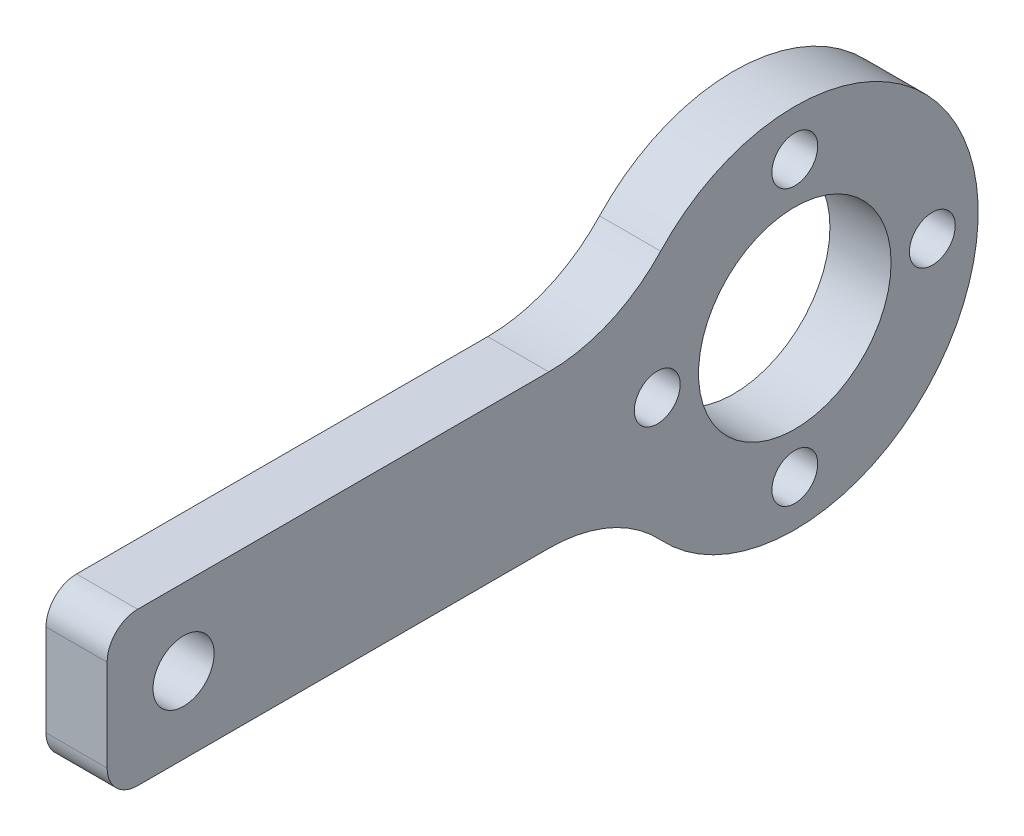
SolidWorks part; units mm, degrees
material "Thornel Mat VMA"
ref_plane "前视基准面" through (0, 0, 0) normal (0, 0, 1) x (1, 0, 0)
ref_plane "上视基准面" through (0, 0, 0) normal (0, 1, 0) x (1, 0, 0)
ref_plane "右视基准面" through (0, 0, 0) normal (1, 0, 0) x (0, 0, -1)
sketch "草图1" plane through (0, 0, 0) normal (1, 0, 0) x (0, 0, -1)
  circle A0 centre (0, 0) radius 9 construction
  circle A1 centre (0, 9) radius 1.5
  circle A2 centre (0, 0) radius 6.3
  circle A3 centre (0, 0) radius 12
  circle A4 centre (9, 0) radius 1.5
  circle A5 centre (0, -9) radius 1.5
  circle A6 centre (-9, 0) radius 1.5
  point P16 (0, 0)
  dimension "D1" = 12.6
  dimension "D2" = 3
  dimension "D3" = 18
  dimension "D4" = 24
  dimension "D5" = 4
extrude "凸台-拉伸1" add sketch "草图1" along normal blind 4
sketch "草图6" plane through (4, 0, 0) normal (1, 0, 0) x (0, 0, -1)
  line L1 (-45, -5) -> (-5, -5)
  line L2 (-45, -5) -> (-45, 5)
  line L3 (-45, 5) -> (-5, 5)
  line L4 (-5, -5) -> (-5, 5)
  circle A0 centre (-40, 0) radius 2
  circle A1 centre (-9, 0) radius 1.5 construction
  circle A2 centre (-9, 0) radius 1.5
  point P5 (-5, 0)
  point P9 (-45, 0)
  dimension "D4" = 4
  dimension "D1" = 5
  dimension "D2" = 10
  dimension "D3" = 40
  dimension "D5" = 5
extrude "凸台-拉伸5" add sketch "草图6" against normal up to surface (4 mm away) up to face at (0, 0, -12)
fillet "圆角1" radius 10 2 edges at (2, -5, 10.9087) (2, 5, 10.9087)
fillet "圆角2" radius 2 2 edges at (2, -5, 45) (2, 5, 45)
sketch "草图7" plane through (4, 0, 0) normal (1, 0, 0) x (0, 0, -1)
  circle A0 centre (0, 0) radius 6.3
extrude "切除-拉伸1" cut sketch "草图7" against normal mid plane 10
